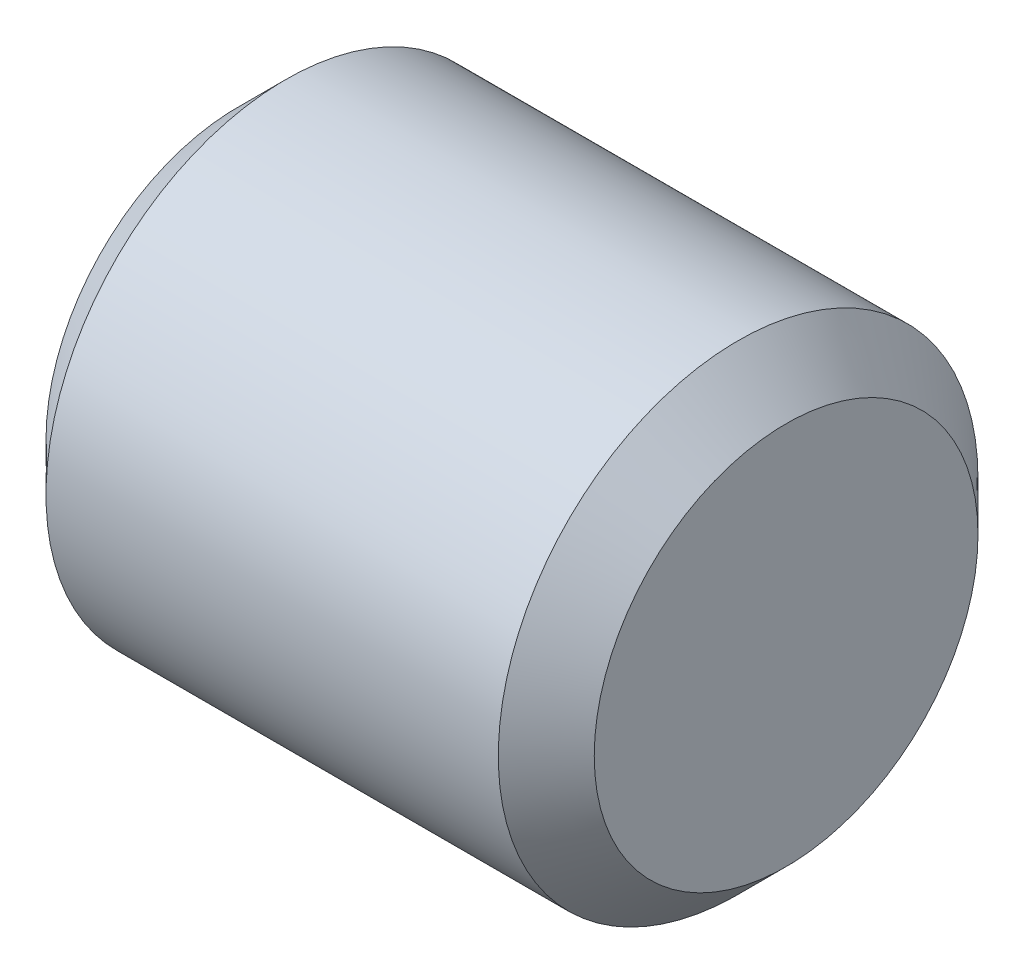
SolidWorks part; units mm, degrees
ref_plane "Front" through (0, 0, 0) normal (0, 0, 1) x (1, 0, 0)
ref_plane "Top" through (0, 0, 0) normal (0, 1, 0) x (1, 0, 0)
ref_plane "Right" through (0, 0, 0) normal (1, 0, 0) x (0, 0, -1)
sketch "Sketch1" plane through (0, 0, 0) normal (0, 0, 1) x (1, 0, 0)
  line L0 (-6.35, 0) -> (6.35, 0) construction
  line L1 (6.35, 5.5562) -> (6.35, -5.5562) construction
  line L2 (-6.35, 5.5562) -> (-6.35, -5.5562) construction
  dimension "Length" = 12.7
  dimension "Diameter" = 11.1125
sketch "Sketch2" plane through (0, 0, 0) normal (1, 0, 0) x (0, 0, -1)
  circle A0 centre (0, 0) radius 5.5562
extrude "Extrude1" add sketch "Sketch2" against normal up to vertex (6.35 mm away) and the other way up to vertex (6.35 mm away) up to point (-6.35, 5.5562, 0) other way up to point (6.35, 5.5562, 0)
chamfer "Chamfer1" distance 1.1113 angle 45 2 edges at (6.35, 0, -5.5562) (-6.35, 0, -5.5562)
equation "\"D1@Chamfer1\" = \"Diameter@Sketch1\"*.1"
